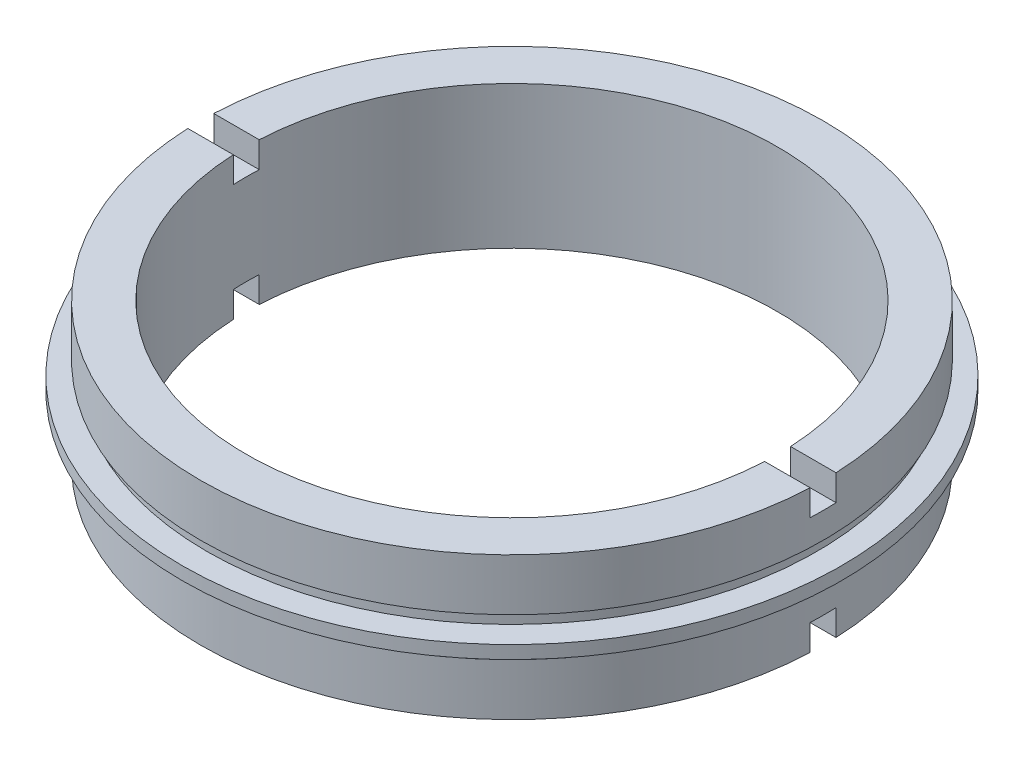
SolidWorks part; units mm, degrees
ref_plane "前视基准面" through (0, 0, 0) normal (0, 0, 1) x (1, 0, 0)
ref_plane "上视基准面" through (0, 0, 0) normal (0, 1, 0) x (1, 0, 0)
ref_plane "右视基准面" through (0, 0, 0) normal (1, 0, 0) x (0, 0, -1)
sketch "草图1" plane through (0, 0, 0) normal (0, 0, 1) x (1, 0, 0)
  line L0 (0, 22.6775) -> (0, 0) construction
  line L1 (-20.5, 11) -> (-24, 11)
  line L2 (-24, 11) -> (-24, 7)
  line L3 (-24, 7) -> (-23.5, 7)
  line L4 (-23.5, 7) -> (-23.5, 6)
  line L5 (-23.5, 6) -> (-25.4, 6)
  line L6 (-25.4, 6) -> (-25.4, 5)
  line L7 (-25.4, 5) -> (-23.5, 5)
  line L8 (-23.5, 5) -> (-23.5, 4)
  line L9 (-23.5, 4) -> (-24, 4)
  line L10 (-24, 4) -> (-24, 0)
  line L11 (-24, 0) -> (-20.5, 0)
  line L12 (-20.5, 0) -> (-20.5, 11)
  point P5 (-25.4, 5.5)
  dimension "D1" = 11
  dimension "D2" = 1
  dimension "D3" = 1
  dimension "D4" = 5
  dimension "D5" = 5
  dimension "D6" = 24
  dimension "D7" = 25.4
  dimension "D8" = 24
  dimension "D9" = 23.5
  dimension "D10" = 23.5
  dimension "D11" = 20.5
  dimension "D12" = 0
revolve "旋转1" add sketch "草图1" angle 360 about L0
cosmetic thread "装饰螺纹线1" parameters "D2"=47
cosmetic thread "装饰螺纹线2" parameters "D2"=47
cosmetic thread "装饰螺纹线3" parameters "D2"=42
sketch "草图2" plane through (0, 0, 0) normal (1, 0, 0) x (0, 0, -1)
  line L0 (20.5, 11) -> (-20.5, 11) construction
  line L1 (-1, 13.594) -> (1, 13.594)
  line L2 (-1, 13.594) -> (-1, 9)
  line L3 (-1, 9) -> (1, 9)
  line L4 (1, 13.594) -> (1, 9)
  line L5 (-1, 2) -> (1, 2)
  line L6 (-1, 2) -> (-1, -4.6679)
  line L7 (-1, -4.6679) -> (1, -4.6679)
  line L8 (1, 2) -> (1, -4.6679)
  dimension "D1" = 2
  dimension "D2" = 1
  dimension "D3" = 2
  dimension "D4" = 1
  dimension "D5" = 2
  dimension "D6" = 2
extrude "切除-拉伸1" cut sketch "草图2" against normal mid plane 79
